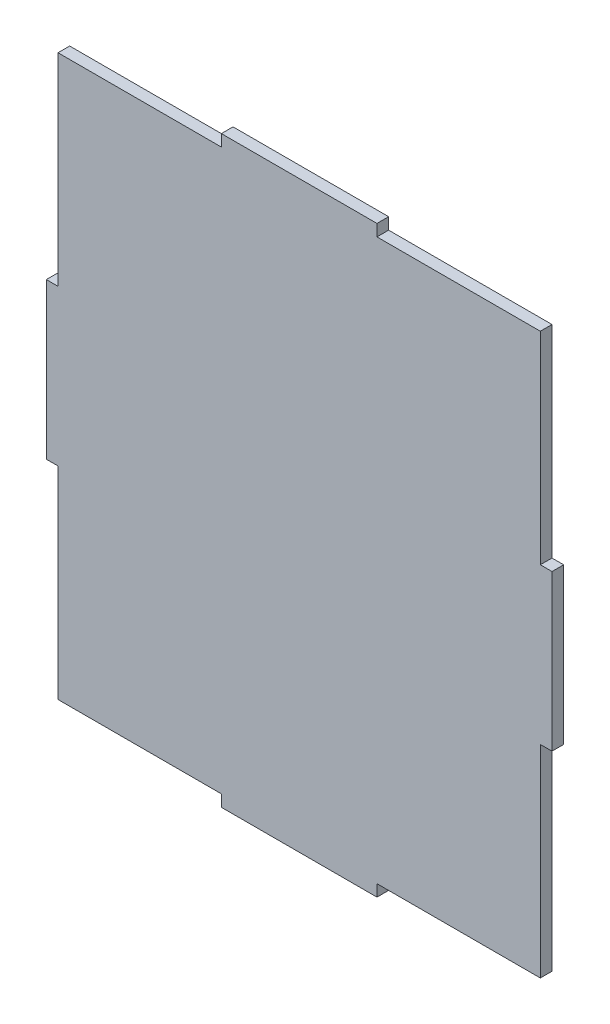
SolidWorks part; units mm, degrees
ref_plane "Plano frontal" through (0, 0, 0) normal (0, 0, 1) x (1, 0, 0)
ref_plane "Plano superior" through (0, 0, 0) normal (0, 1, 0) x (1, 0, 0)
ref_plane "Plano direito" through (0, 0, 0) normal (1, 0, 0) x (0, 0, -1)
sketch "Esboço2" plane through (0, 0, 0) normal (0, 0, 1) x (1, 0, 0)
  line L0 (-60.4535, 66.8449) -> (63.5465, 66.8449)
  line L1 (-60.4535, 66.8449) -> (-60.4535, -77.1551)
  line L2 (-60.4535, -77.1551) -> (63.5465, -77.1551)
  line L3 (63.5465, 66.8449) -> (63.5465, -77.1551)
  line L4 (63.5465, 14.8449) -> (66.5465, 14.8449)
  line L5 (63.5465, 14.8449) -> (63.5465, -25.1551)
  line L6 (63.5465, -25.1551) -> (66.5465, -25.1551)
  line L7 (66.5465, 14.8449) -> (66.5465, -25.1551)
  line L8 (-18.4535, 69.8449) -> (21.5465, 69.8449)
  line L9 (-18.4535, 69.8449) -> (-18.4535, 66.8449)
  line L10 (-18.4535, 66.8449) -> (21.5465, 66.8449)
  line L11 (21.5465, 69.8449) -> (21.5465, 66.8449)
  line L12 (-63.4535, 14.8449) -> (-60.4535, 14.8449)
  line L13 (-63.4535, 14.8449) -> (-63.4535, -25.1551)
  line L14 (-63.4535, -25.1551) -> (-60.4535, -25.1551)
  line L15 (-60.4535, 14.8449) -> (-60.4535, -25.1551)
  line L16 (-18.4535, -80.1551) -> (21.5465, -80.1551)
  line L17 (-18.4535, -80.1551) -> (-18.4535, -77.1551)
  line L18 (-18.4535, -77.1551) -> (21.5465, -77.1551)
  line L19 (21.5465, -80.1551) -> (21.5465, -77.1551)
extrude "Ressalto-extrusão2" add sketch "Esboço2" along normal blind 3 contours L3 L0 L1 L2 | L13 L14 L15 L12 | L8 L11 L10 L9 | L7 L6 L5 L4 | L16 L19 L18 L17
sketch "Esboço3" plane through (0, 0, 0) normal (0, 0, -1) x (-1, 0, 0)
  line L0 (-13.138, 5.9406) -> (9.4535, 5.9406)
  line L1 (-13.138, 5.9406) -> (-13.138, -16.6508)
  line L2 (-13.138, -16.6508) -> (9.4535, -16.6508)
  line L3 (9.4535, 5.9406) -> (9.4535, -16.6508)
  line L4 (-17.3381, 10.9365) -> (14.9535, 10.9365)
  line L5 (-17.3381, 10.9365) -> (-17.3381, -21.3551)
  line L6 (-17.3381, -21.3551) -> (14.9535, -21.3551)
  line L7 (14.9535, 10.9365) -> (14.9535, -21.3551)
  line L10 (-21.5465, -77.1551) -> (-63.5465, -77.1551) construction
  line L15 (60.4535, 66.8449) -> (60.4535, 14.8449) construction
  circle A0 centre (-1.5465, -5.3551) radius 11.2957
  circle A1 centre (-1.5465, -5.3551) radius 16.1458
  point P11 (0, 0)
  dimension "D2" = 32.2915
  dimension "D3" = 62
  dimension "D6" = 16
  dimension "D1" = 45.5
  dimension "D4" = 11
  dimension "D5" = 55.8
